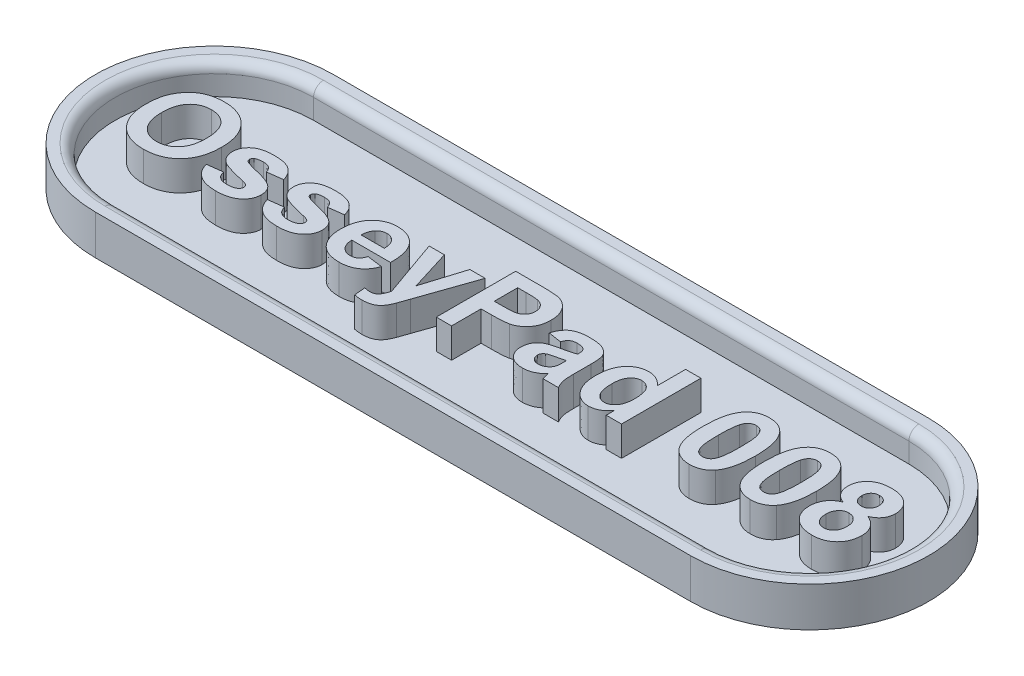
SolidWorks part; units mm, degrees
ref_plane "Front Plane" through (0, 0, 0) normal (0, 0, 1) x (1, 0, 0)
ref_plane "Top Plane" through (0, 0, 0) normal (0, 1, 0) x (1, 0, 0)
ref_plane "Right Plane" through (0, 0, 0) normal (1, 0, 0) x (0, 0, -1)
sketch "Sketch1" plane through (0, 0, 0) normal (0, 1, 0) x (1, 0, 0)
  line L0 (-15, 0) -> (15, 0) construction
  line L1 (-15, 6) -> (15, 6)
  line L2 (-15, -6) -> (15, -6)
  arc A0 (-15, 6) -> (-15, -6) centre (-15, 0) ccw
  arc A1 (15, -6) -> (15, 6) centre (15, 0) ccw
  point P2 (0, 0)
  dimension "D1" = 12
  dimension "D2" = 30
extrude "Boss-Extrude1" add sketch "Sketch1" along normal blind 2
sketch "Sketch2" plane through (0, 2, 0) normal (0, 1, 0) x (1, 0, 0)
  line L0 (-15, 0) -> (15, 0) construction
  line L1 (-15, 5) -> (15, 5)
  line L2 (-15, -5) -> (15, -5)
  arc A0 (-15, 5) -> (-15, -5) centre (-15, 0) ccw
  arc A1 (15, -5) -> (15, 5) centre (15, 0) ccw
  point P2 (0, 0)
  dimension "D1" = 30
  dimension "D2" = 10
extrude "Cut-Extrude1" cut sketch "Sketch2" against normal blind 1.5
sketch "Sketch3" plane through (0, 0.5, 0) normal (0, 1, 0) x (1, 0, 0)
  line L0 (-21, -1.995) -> (21, -1.995) construction
  line L1 (0, -8.7006) -> (0, 6.9821) construction
  line L3 (-15, -5) -> (15, -5) construction
  text T0 "OsseyPad 008" font "Arial" height 4
  dimension "D1" = 3.005
extrude "Boss-Extrude2" add sketch "Sketch3" along normal blind 1.5
fillet "Fillet1" radius 0.5 4 edges at (0, 2, -5) (20, 2, 0) (0, 2, 5) (-20, 2, 0)
